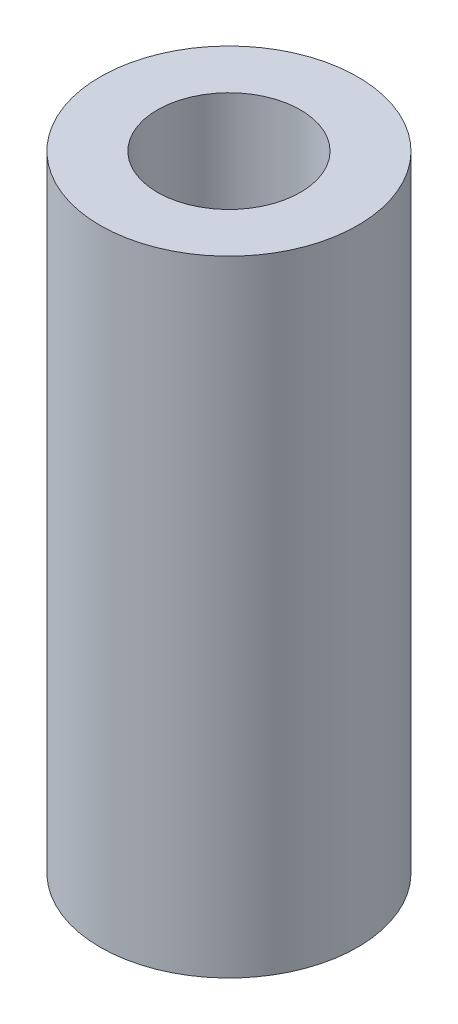
SolidWorks part; units mm, degrees
ref_plane "Front Plane" through (0, 0, 0) normal (0, 0, 1) x (1, 0, 0)
ref_plane "Top Plane" through (0, 0, 0) normal (0, 1, 0) x (1, 0, 0)
ref_plane "Right Plane" through (0, 0, 0) normal (1, 0, 0) x (0, 0, -1)
sketch "Sketch1" plane through (0, 0, 0) normal (0, 1, 0) x (1, 0, 0)
  circle A0 centre (0, 0) radius 2.5
  circle A1 centre (0, 0) radius 4.5
  dimension "D1" = 5
  dimension "D2" = 9
extrude "Boss-Extrude1" add sketch "Sketch1" along normal blind 21.85
